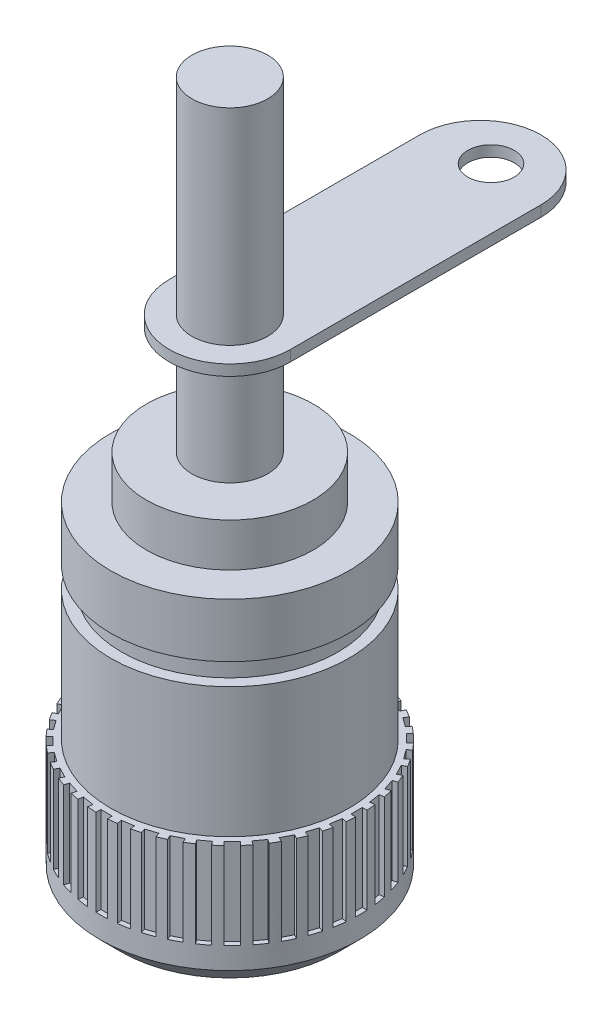
SolidWorks part; units mm, degrees
ref_plane "Front Plane" through (0, 0, 0) normal (0, 0, 1) x (1, 0, 0)
ref_plane "Top Plane" through (0, 0, 0) normal (0, 1, 0) x (1, 0, 0)
ref_plane "Right Plane" through (0, 0, 0) normal (1, 0, 0) x (0, 0, -1)
sketch "Sketch1" plane through (0, 0, 0) normal (0, 1, 0) x (1, 0, 0)
  circle A0 centre (0, 0) radius 6
  dimension "D1" = 12
extrude "Boss-Extrude1" add sketch "Sketch1" along normal blind 12
sketch "Sketch2" plane through (0, 12, 0) normal (0, 1, 0) x (1, 0, 0)
  circle A0 centre (0, 0) radius 5.5
  circle A1 centre (0, 0) radius 8.1182
  dimension "D1" = 11
extrude "Cut-Extrude1" cut sketch "Sketch2" against normal blind 6
chamfer "Chamfer1" distance 1 angle 45 1 edges at (0, 0, 6)
sketch "Sketch3" plane through (0, 0, 0) normal (0, -1, 0) x (1, 0, 0)
  circle A0 centre (0, 0) radius 3.25
  dimension "D1" = 6.5
extrude "Cut-Extrude2" cut sketch "Sketch3" against normal blind 6
sketch "Sketch5" plane through (0, 12, 0) normal (0, 1, 0) x (1, 0, 0)
  circle A0 centre (0, 0) radius 5
  dimension "D1" = 10
extrude "Boss-Extrude2" add sketch "Sketch5" along normal blind 1
sketch "Sketch6" plane through (0, 13, 0) normal (0, 1, 0) x (1, 0, 0)
  circle A0 centre (0, 0) radius 5.5
extrude "Boss-Extrude3" add sketch "Sketch6" along normal blind 2.5
sketch "Sketch7" plane through (0, 6, 0) normal (0, -1, 0) x (1, 0, 0)
  circle A0 centre (0, 0) radius 2.7165
  circle A1 centre (0, 0) radius 2.4857
extrude "Boss-Extrude4" add sketch "Sketch7" along normal blind 4.5
sketch "Sketch8" plane through (0, 15.5, 0) normal (0, 1, 0) x (1, 0, 0)
  circle A0 centre (0, 0) radius 3.85
  dimension "D1" = 7.7
extrude "Boss-Extrude5" add sketch "Sketch8" along normal blind 2
sketch "Sketch9" plane through (0, 17.5, 0) normal (0, 1, 0) x (1, 0, 0)
  circle A0 centre (0, 0) radius 1.75
  dimension "D1" = 3.5
extrude "Boss-Extrude6" add sketch "Sketch9" along normal blind 15
sketch "Sketch10" plane through (0, 17.5, 0) normal (0, 1, 0) x (1, 0, 0)
  line L0 (0, 0) -> (0, 11.572) construction
  line L1 (-2.7978, 0) -> (-2.7978, 11.572)
  line L2 (2.7978, 0) -> (2.7978, 11.572)
  arc A0 (-2.7978, 0) -> (2.7978, 0) centre (0, 0) ccw
  arc A1 (2.7978, 11.572) -> (-2.7978, 11.572) centre (0, 11.572) ccw
  point P3 (0, 5.786)
  point P8 (0, 11.572)
extrude "Boss-Extrude7" add sketch "Sketch10" along normal blind 0.5 from offset 5
sketch "Sketch11" plane through (0, 22.5, 0) normal (0, -1, 0) x (1, 0, 0)
  circle A0 centre (0, -12.0618) radius 1.0712
extrude "Cut-Extrude3" cut sketch "Sketch11" against normal blind 0.5
sketch "Sketch12" plane through (0, 0, 0) normal (0, -1, 0) x (1, 0, 0)
  line L0 (0.8247, 6.3742) -> (0.723, 5.7316)
  line L1 (-0.1826, 6.4247) -> (0.3452, 6.4247)
  line L2 (-0.1826, 6.4247) -> (-0.1826, 5.7742)
  line L3 (-0.1826, 5.7742) -> (0.3452, 5.7742)
  line L4 (0.3452, 6.4247) -> (0.3452, 5.7742)
  line L5 (0.8247, 6.3742) -> (1.346, 6.2916)
  line L6 (1.346, 6.2916) -> (1.2443, 5.6491)
  line L7 (0.723, 5.7316) -> (1.2443, 5.6491)
  line L8 (1.8117, 6.1667) -> (1.6107, 5.548)
  line L9 (1.8117, 6.1667) -> (2.3137, 6.0036)
  line L10 (2.3137, 6.0036) -> (2.1127, 5.3849)
  line L11 (1.6107, 5.548) -> (2.1127, 5.3849)
  line L12 (2.7541, 5.8074) -> (2.4587, 5.2277)
  line L13 (2.7541, 5.8074) -> (3.2244, 5.5677)
  line L14 (3.2244, 5.5677) -> (2.929, 4.9881)
  line L15 (2.4587, 5.2277) -> (2.929, 4.9881)
  line L16 (3.6287, 5.305) -> (3.2463, 4.7787)
  line L17 (3.6287, 5.305) -> (4.0557, 4.9948)
  line L18 (4.0557, 4.9948) -> (3.6733, 4.4685)
  line L19 (3.2463, 4.7787) -> (3.6733, 4.4685)
  line L20 (4.4139, 4.6721) -> (3.9539, 4.2121)
  line L21 (4.4139, 4.6721) -> (4.7871, 4.2989)
  line L22 (4.7871, 4.2989) -> (4.3271, 3.8388)
  line L23 (3.9539, 4.2121) -> (4.3271, 3.8388)
  line L24 (5.0904, 3.9241) -> (4.5641, 3.5417)
  line L25 (5.0904, 3.9241) -> (5.4006, 3.4971)
  line L26 (5.4006, 3.4971) -> (4.8743, 3.1147)
  line L27 (4.5641, 3.5417) -> (4.8743, 3.1147)
  line L28 (5.6416, 3.0794) -> (5.0619, 2.7841)
  line L29 (5.6416, 3.0794) -> (5.8812, 2.6092)
  line L30 (5.8812, 2.6092) -> (5.3016, 2.3138)
  line L31 (5.0619, 2.7841) -> (5.3016, 2.3138)
  line L32 (6.0539, 2.159) -> (5.4351, 1.958)
  line L33 (6.0539, 2.159) -> (6.217, 1.657)
  line L34 (6.217, 1.657) -> (5.5983, 1.456)
  line L35 (5.4351, 1.958) -> (5.5983, 1.456)
  line L36 (6.3171, 1.1854) -> (5.6745, 1.0836)
  line L37 (6.3171, 1.1854) -> (6.3996, 0.6641)
  line L38 (6.3996, 0.6641) -> (5.7571, 0.5623)
  line L39 (5.6745, 1.0836) -> (5.7571, 0.5623)
  line L40 (6.4247, 0.1826) -> (5.7742, 0.1826)
  line L41 (6.4247, 0.1826) -> (6.4247, -0.3452)
  line L42 (6.4247, -0.3452) -> (5.7742, -0.3452)
  line L43 (5.7742, 0.1826) -> (5.7742, -0.3452)
  line L44 (6.3742, -0.8247) -> (5.7316, -0.723)
  line L45 (6.3742, -0.8247) -> (6.2916, -1.346)
  line L46 (6.2916, -1.346) -> (5.6491, -1.2443)
  line L47 (5.7316, -0.723) -> (5.6491, -1.2443)
  line L48 (6.1667, -1.8117) -> (5.548, -1.6107)
  line L49 (6.1667, -1.8117) -> (6.0036, -2.3137)
  line L50 (6.0036, -2.3137) -> (5.3849, -2.1127)
  line L51 (5.548, -1.6107) -> (5.3849, -2.1127)
  line L52 (5.8074, -2.7541) -> (5.2277, -2.4587)
  line L53 (5.8074, -2.7541) -> (5.5677, -3.2244)
  line L54 (5.5677, -3.2244) -> (4.9881, -2.929)
  line L55 (5.2277, -2.4587) -> (4.9881, -2.929)
  line L56 (5.305, -3.6287) -> (4.7787, -3.2463)
  line L57 (5.305, -3.6287) -> (4.9948, -4.0557)
  line L58 (4.9948, -4.0557) -> (4.4685, -3.6733)
  line L59 (4.7787, -3.2463) -> (4.4685, -3.6733)
  line L60 (4.6721, -4.4139) -> (4.2121, -3.9539)
  line L61 (4.6721, -4.4139) -> (4.2989, -4.7871)
  line L62 (4.2989, -4.7871) -> (3.8388, -4.3271)
  line L63 (4.2121, -3.9539) -> (3.8388, -4.3271)
  line L64 (3.9241, -5.0904) -> (3.5417, -4.5641)
  line L65 (3.9241, -5.0904) -> (3.4971, -5.4006)
  line L66 (3.4971, -5.4006) -> (3.1147, -4.8743)
  line L67 (3.5417, -4.5641) -> (3.1147, -4.8743)
  line L68 (3.0794, -5.6416) -> (2.7841, -5.0619)
  line L69 (3.0794, -5.6416) -> (2.6092, -5.8812)
  line L70 (2.6092, -5.8812) -> (2.3138, -5.3016)
  line L71 (2.7841, -5.0619) -> (2.3138, -5.3016)
  line L72 (2.159, -6.0539) -> (1.958, -5.4351)
  line L73 (2.159, -6.0539) -> (1.657, -6.217)
  line L74 (1.657, -6.217) -> (1.456, -5.5983)
  line L75 (1.958, -5.4351) -> (1.456, -5.5983)
  line L76 (1.1854, -6.3171) -> (1.0836, -5.6745)
  line L77 (1.1854, -6.3171) -> (0.6641, -6.3996)
  line L78 (0.6641, -6.3996) -> (0.5623, -5.7571)
  line L79 (1.0836, -5.6745) -> (0.5623, -5.7571)
  line L80 (0.1826, -6.4247) -> (0.1826, -5.7742)
  line L81 (0.1826, -6.4247) -> (-0.3452, -6.4247)
  line L82 (-0.3452, -6.4247) -> (-0.3452, -5.7742)
  line L83 (0.1826, -5.7742) -> (-0.3452, -5.7742)
  line L84 (-0.8247, -6.3742) -> (-0.723, -5.7316)
  line L85 (-0.8247, -6.3742) -> (-1.346, -6.2916)
  line L86 (-1.346, -6.2916) -> (-1.2443, -5.6491)
  line L87 (-0.723, -5.7316) -> (-1.2443, -5.6491)
  line L88 (-1.8117, -6.1667) -> (-1.6107, -5.548)
  line L89 (-1.8117, -6.1667) -> (-2.3137, -6.0036)
  line L90 (-2.3137, -6.0036) -> (-2.1127, -5.3849)
  line L91 (-1.6107, -5.548) -> (-2.1127, -5.3849)
  line L92 (-2.7541, -5.8074) -> (-2.4587, -5.2277)
  line L93 (-2.7541, -5.8074) -> (-3.2244, -5.5677)
  line L94 (-3.2244, -5.5677) -> (-2.929, -4.9881)
  line L95 (-2.4587, -5.2277) -> (-2.929, -4.9881)
  line L96 (-3.6287, -5.305) -> (-3.2463, -4.7787)
  line L97 (-3.6287, -5.305) -> (-4.0557, -4.9948)
  line L98 (-4.0557, -4.9948) -> (-3.6733, -4.4685)
  line L99 (-3.2463, -4.7787) -> (-3.6733, -4.4685)
  line L100 (-4.4139, -4.6721) -> (-3.9539, -4.2121)
  line L101 (-4.4139, -4.6721) -> (-4.7871, -4.2989)
  line L102 (-4.7871, -4.2989) -> (-4.3271, -3.8388)
  line L103 (-3.9539, -4.2121) -> (-4.3271, -3.8388)
  line L104 (-5.0904, -3.9241) -> (-4.5641, -3.5417)
  line L105 (-5.0904, -3.9241) -> (-5.4006, -3.4971)
  line L106 (-5.4006, -3.4971) -> (-4.8743, -3.1147)
  line L107 (-4.5641, -3.5417) -> (-4.8743, -3.1147)
  line L108 (-5.6416, -3.0794) -> (-5.0619, -2.7841)
  line L109 (-5.6416, -3.0794) -> (-5.8812, -2.6092)
  line L110 (-5.8812, -2.6092) -> (-5.3016, -2.3138)
  line L111 (-5.0619, -2.7841) -> (-5.3016, -2.3138)
  line L112 (-6.0539, -2.159) -> (-5.4351, -1.958)
  line L113 (-6.0539, -2.159) -> (-6.217, -1.657)
  line L114 (-6.217, -1.657) -> (-5.5983, -1.456)
  line L115 (-5.4351, -1.958) -> (-5.5983, -1.456)
  line L116 (-6.3171, -1.1854) -> (-5.6745, -1.0836)
  line L117 (-6.3171, -1.1854) -> (-6.3996, -0.6641)
  line L118 (-6.3996, -0.6641) -> (-5.7571, -0.5623)
  line L119 (-5.6745, -1.0836) -> (-5.7571, -0.5623)
  line L120 (-6.4247, -0.1826) -> (-5.7742, -0.1826)
  line L121 (-6.4247, -0.1826) -> (-6.4247, 0.3452)
  line L122 (-6.4247, 0.3452) -> (-5.7742, 0.3452)
  line L123 (-5.7742, -0.1826) -> (-5.7742, 0.3452)
  line L124 (-6.3742, 0.8247) -> (-5.7316, 0.723)
  line L125 (-6.3742, 0.8247) -> (-6.2916, 1.346)
  line L126 (-6.2916, 1.346) -> (-5.6491, 1.2443)
  line L127 (-5.7316, 0.723) -> (-5.6491, 1.2443)
  line L128 (-6.1667, 1.8117) -> (-5.548, 1.6107)
  line L129 (-6.1667, 1.8117) -> (-6.0036, 2.3137)
  line L130 (-6.0036, 2.3137) -> (-5.3849, 2.1127)
  line L131 (-5.548, 1.6107) -> (-5.3849, 2.1127)
  line L132 (-5.8074, 2.7541) -> (-5.2277, 2.4587)
  line L133 (-5.8074, 2.7541) -> (-5.5677, 3.2244)
  line L134 (-5.5677, 3.2244) -> (-4.9881, 2.929)
  line L135 (-5.2277, 2.4587) -> (-4.9881, 2.929)
  line L136 (-5.305, 3.6287) -> (-4.7787, 3.2463)
  line L137 (-5.305, 3.6287) -> (-4.9948, 4.0557)
  line L138 (-4.9948, 4.0557) -> (-4.4685, 3.6733)
  line L139 (-4.7787, 3.2463) -> (-4.4685, 3.6733)
  line L140 (-4.6721, 4.4139) -> (-4.2121, 3.9539)
  line L141 (-4.6721, 4.4139) -> (-4.2989, 4.7871)
  line L142 (-4.2989, 4.7871) -> (-3.8388, 4.3271)
  line L143 (-4.2121, 3.9539) -> (-3.8388, 4.3271)
  line L144 (-3.9241, 5.0904) -> (-3.5417, 4.5641)
  line L145 (-3.9241, 5.0904) -> (-3.4971, 5.4006)
  line L146 (-3.4971, 5.4006) -> (-3.1147, 4.8743)
  line L147 (-3.5417, 4.5641) -> (-3.1147, 4.8743)
  line L148 (-3.0794, 5.6416) -> (-2.7841, 5.0619)
  line L149 (-3.0794, 5.6416) -> (-2.6092, 5.8812)
  line L150 (-2.6092, 5.8812) -> (-2.3138, 5.3016)
  line L151 (-2.7841, 5.0619) -> (-2.3138, 5.3016)
  line L152 (-2.159, 6.0539) -> (-1.958, 5.4351)
  line L153 (-2.159, 6.0539) -> (-1.657, 6.217)
  line L154 (-1.657, 6.217) -> (-1.456, 5.5983)
  line L155 (-1.958, 5.4351) -> (-1.456, 5.5983)
  line L156 (-1.1854, 6.3171) -> (-1.0836, 5.6745)
  line L157 (-1.1854, 6.3171) -> (-0.6641, 6.3996)
  line L158 (-0.6641, 6.3996) -> (-0.5623, 5.7571)
  line L159 (-1.0836, 5.6745) -> (-0.5623, 5.7571)
  point P162 (0, 0)
  dimension "D1" = 40
extrude "Cut-Extrude4" cut sketch "Sketch12" against normal blind 8.5 from offset 2
